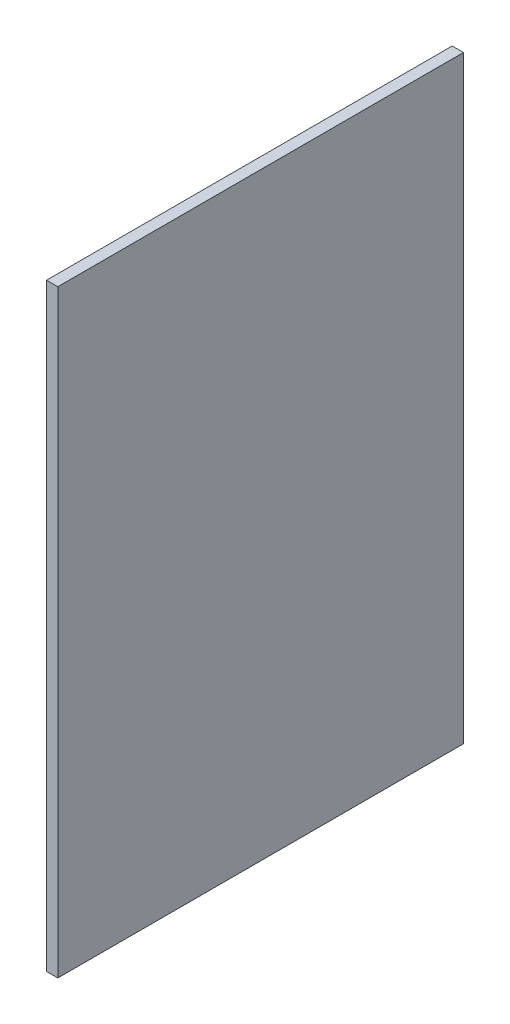
SolidWorks part; units mm, degrees
ref_plane "Front Plane" through (0, 0, 0) normal (0, 0, 1) x (1, 0, 0)
ref_plane "Top Plane" through (0, 0, 0) normal (0, 1, 0) x (1, 0, 0)
ref_plane "Right Plane" through (0, 0, 0) normal (1, 0, 0) x (0, 0, -1)
sketch "Sketch1" plane through (0, 0, 0) normal (1, 0, 0) x (0, 0, -1)
  line L1 (0, 0) -> (576, 0)
  line L2 (0, 0) -> (0, 850)
  line L3 (0, 850) -> (576, 850)
  line L4 (576, 0) -> (576, 850)
  dimension "D1" = 850
  dimension "D2" = 576
extrude "Extrude1" add sketch "Sketch1" against normal blind 16
